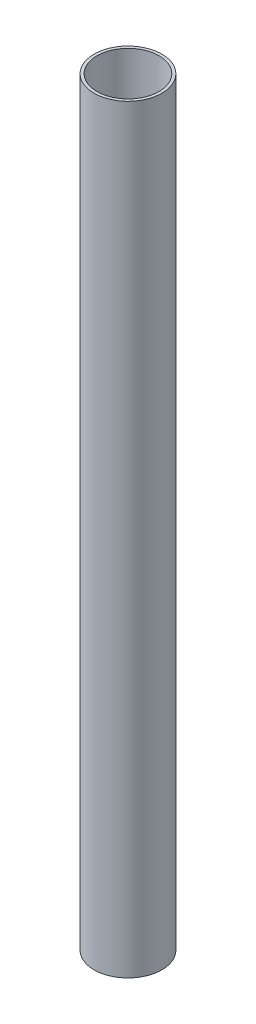
SolidWorks part; units mm, degrees
ref_plane "Front Plane" through (0, 0, 0) normal (0, 0, 1) x (1, 0, 0)
ref_plane "Top Plane" through (0, 0, 0) normal (0, 1, 0) x (1, 0, 0)
ref_plane "Right Plane" through (0, 0, 0) normal (1, 0, 0) x (0, 0, -1)
sketch "Sketch1" plane through (0, 0, 0) normal (0, 1, 0) x (1, 0, 0)
  circle A0 centre (0, 0) radius 14.732
extrude "Boss-Extrude1" add sketch "Sketch1" along normal blind 330.2
sketch "Sketch2" plane through (0, 330.2, 0) normal (0, 1, 0) x (1, 0, 0)
  circle A0 centre (0, 0) radius 13.4944
extrude "Cut-Extrude1" cut sketch "Sketch2" against normal blind 330.2
